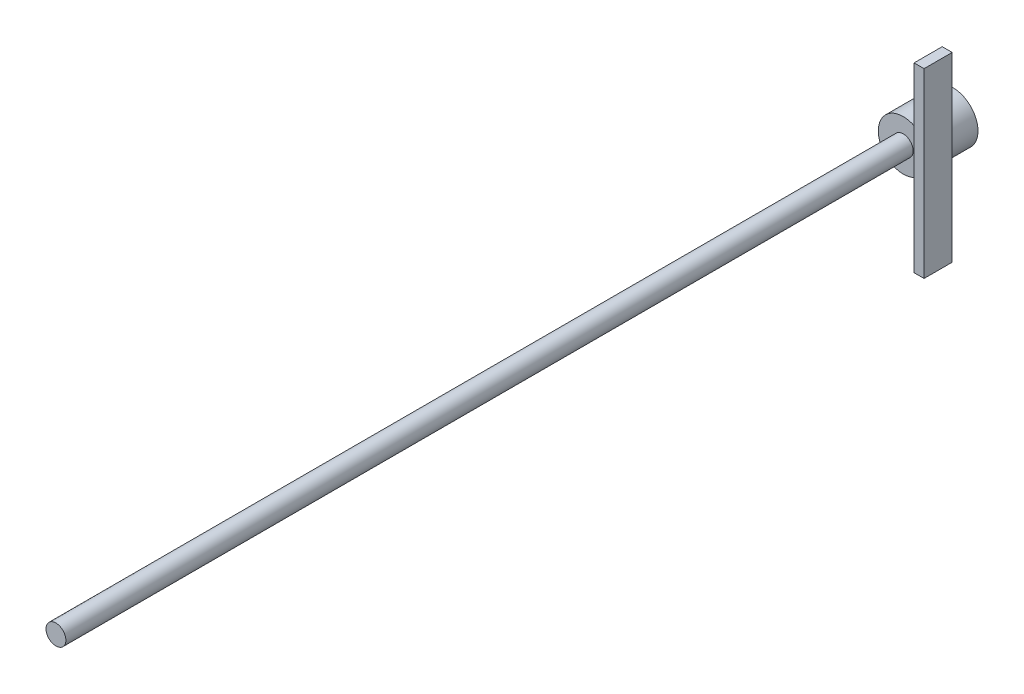
SolidWorks part; units mm, degrees
ref_plane "Plan de face" through (0, 0, 0) normal (0, 0, 1) x (1, 0, 0)
ref_plane "Plan de dessus" through (0, 0, 0) normal (0, 1, 0) x (1, 0, 0)
ref_plane "Plan de droite" through (0, 0, 0) normal (1, 0, 0) x (0, 0, -1)
sketch "Esquisse1" plane through (0, 0, 0) normal (0, 0, 1) x (1, 0, 0)
  circle A0 centre (0, 0) radius 2.5
  dimension "D1" = 5
extrude "Boss.-Extru.1" add sketch "Esquisse1" along normal blind 5
sketch "Esquisse2" plane through (0, 0, 0) normal (0, 0, 1) x (1, 0, 0)
  circle A0 centre (0, 0) radius 0.9974
extrude "Boss.-Extru.2" add sketch "Esquisse2" along normal blind 90
ref_plane "Plan1" through (2.5, 0, 0) normal (1, 0, 0) x (0, 0, -1)
sketch "Esquisse3" plane through (2.5, 0, 0) normal (1, 0, 0) x (0, 0, -1)
  line L3 (-3.5906, 9.1159) -> (-6.4094, 9.1159)
  line L4 (-6.4094, -9.1159) -> (-6.4094, 9.1159)
  line L5 (-3.5906, -9.1159) -> (-3.5906, 9.1159)
  line L6 (-3.5906, -9.1159) -> (-6.4094, -9.1159)
  point P9 (-3.5906, 0)
extrude "Boss.-Extru.3" add sketch "Esquisse3" along normal blind 1 separate body
